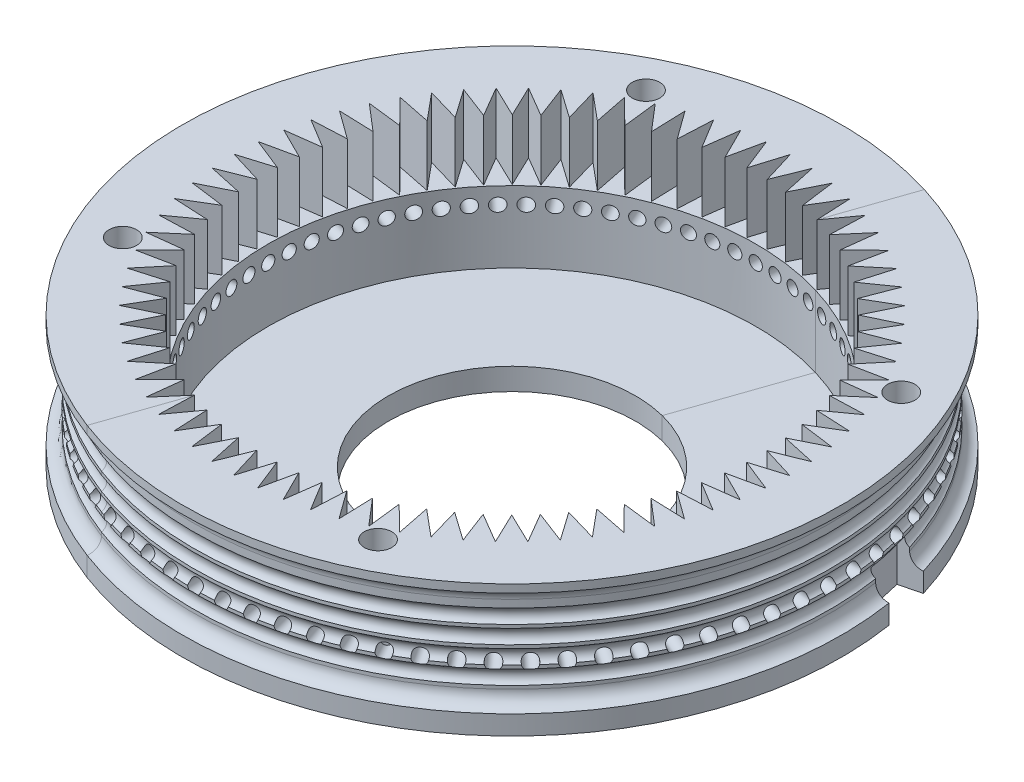
SolidWorks part; units mm, degrees
ref_plane "Front Plane" through (0, 0, 0) normal (0, 0, 1) x (1, 0, 0)
ref_plane "Top Plane" through (0, 0, 0) normal (0, 1, 0) x (1, 0, 0)
ref_plane "Right Plane" through (0, 0, 0) normal (1, 0, 0) x (0, 0, -1)
sketch "Sketch1" plane through (0, 0, 0) normal (0, 1, 0) x (1, 0, 0)
  circle A1 centre (0, 0) radius 23
extrude "Boss-Extrude1" add sketch "Sketch1" against normal blind 2
sketch "Sketch2" plane through (0, 0, 0) normal (0, 1, 0) x (1, 0, 0)
  circle A0 centre (0, 0) radius 30
  circle A1 centre (0, 0) radius 22.2
extrude "Boss-Extrude2" add sketch "Sketch2" along normal blind 12
sketch "Sketch3" plane through (0, 0, 0) normal (0, 1, 0) x (1, 0, 0)
  circle A0 centre (0, 0) radius 11.25
extrude "Cut-Extrude1" cut sketch "Sketch3" against normal blind 10 contours A0
ref_plane "Plane1" through (0, 12, 0) normal (0, 1, 0) x (1, 0, 0)
ref_plane "Plane2" through (0, -2, 0) normal (0, -1, 0) x (-1, 0, 0)
ref_plane "Plane3" through (0, 0, 0) normal (0, -1, 0) x (-1, 0, 0)
sketch "Sketch6" plane through (0, 0, 0) normal (1, 0, 0) x (0, 0, -1)
  line L0 (30.0526, 11.27) -> (30.6112, 11.27)
  line L1 (30.6112, 11.27) -> (30.6112, 1.7441)
  line L2 (30.6112, 6.507) -> (36.0017, 6.507) construction
  line L3 (30.6112, 1.7441) -> (30.0526, 1.7441)
  line L4 (28.9711, 9.6701) -> (28.9711, 9.363)
  line L5 (28.9711, 8.0701) -> (28.9711, 7.763)
  line L6 (28.9711, 6.4701) -> (28.9711, 6.163)
  line L7 (28.9711, 4.8701) -> (28.9711, 4.563)
  line L8 (28.9711, 3.2701) -> (28.9711, 2.963)
  line L9 (28.9711, 10.051) -> (28.9711, 9.6701)
  arc A0 (28.9711, 10.051) -> (30.0526, 11.27) centre (30.1988, 10.051) cw
  arc A1 (28.9711, 9.363) -> (28.9711, 8.0701) centre (29.3513, 8.7166) ccw
  arc A2 (28.9711, 7.763) -> (28.9711, 6.4701) centre (29.3513, 7.1166) ccw
  arc A3 (28.9711, 6.163) -> (28.9711, 4.8701) centre (29.3513, 5.5166) ccw
  arc A4 (28.9711, 4.563) -> (28.9711, 3.2701) centre (29.3513, 3.9166) ccw
  arc A5 (28.9711, 2.963) -> (30.0526, 1.7441) centre (30.1988, 2.963) ccw
  dimension "D2" = 1.6
  dimension "D3" = 1.6
  dimension "D4" = 1.6
ref_axis "Axis1" through (0, -2, 0) along (0, 1, 0)
sketch "Sketch10" plane through (0, 12, 0) normal (0, 1, 0) x (1, 0, 0)
  line L0 (8.2003, -23.949) -> (8.0956, -20.7964)
  line L1 (8.2003, -23.949) -> (7.2077, -21.0502) construction
  line L2 (8.2003, -23.949) -> (6.3506, -21.3939)
  line L3 (6.1946, -24.5444) -> (6.3506, -21.3939)
  line L5 (6.1946, -24.5444) -> (4.5623, -21.8453)
  line L6 (4.1466, -24.9721) -> (4.5623, -21.8453)
  line L7 (4.1466, -24.9721) -> (2.7427, -22.1474)
  line L8 (2.0703, -25.2292) -> (2.7427, -22.1474)
  line L9 (2.0703, -25.2292) -> (0.9044, -22.2983)
  line L10 (-0.0202, -25.314) -> (0.9044, -22.2983)
  line L11 (-0.0202, -25.314) -> (-0.9401, -22.2968)
  line L12 (-2.1106, -25.2259) -> (-0.9401, -22.2968)
  line L13 (-2.1106, -25.2259) -> (-2.7781, -22.143)
  line L14 (-4.1865, -24.9654) -> (-2.7781, -22.143)
  line L15 (-4.1865, -24.9654) -> (-4.5972, -21.838)
  line L16 (-6.2338, -24.5345) -> (-4.5972, -21.838)
  line L17 (-6.2338, -24.5345) -> (-6.3848, -21.3837)
  line L18 (-8.2386, -23.9359) -> (-6.3848, -21.3837)
  line L19 (-8.2386, -23.9359) -> (-8.1289, -20.7835)
  line L20 (-10.1871, -23.1738) -> (-8.1289, -20.7835)
  line L21 (-10.1871, -23.1738) -> (-9.8174, -20.0412)
  line L22 (-12.0659, -22.2534) -> (-9.8174, -20.0412)
  line L23 (-12.0659, -22.2534) -> (-11.4389, -19.162)
  line L24 (-13.8624, -21.181) -> (-11.4389, -19.162)
  line L25 (-13.8624, -21.181) -> (-12.9822, -18.152)
  line L26 (-15.5642, -19.9639) -> (-12.9822, -18.152)
  line L27 (-15.5642, -19.9639) -> (-14.4368, -17.0179)
  line L28 (-17.1596, -18.6104) -> (-14.4368, -17.0179)
  line L29 (-17.1596, -18.6104) -> (-15.7928, -15.7676)
  line L30 (-18.6378, -17.1298) -> (-15.7928, -15.7676)
  line L31 (-18.6378, -17.1298) -> (-17.041, -14.4096)
  line L32 (-19.9887, -15.5322) -> (-17.041, -14.4096)
  line L33 (-19.9887, -15.5322) -> (-18.1727, -12.9531)
  line L34 (-21.2031, -13.8285) -> (-18.1727, -12.9531)
  line L35 (-21.2031, -13.8285) -> (-19.1803, -11.4082)
  line L36 (-22.2726, -12.0304) -> (-19.1803, -11.4082)
  line L37 (-22.2726, -12.0304) -> (-20.0569, -9.7854)
  line L38 (-23.19, -10.15) -> (-20.0569, -9.7854)
  line L39 (-23.19, -10.15) -> (-20.7964, -8.0956)
  line L40 (-23.949, -8.2003) -> (-20.7964, -8.0956)
  line L41 (-23.949, -8.2003) -> (-21.3939, -6.3506)
  line L42 (-24.5444, -6.1946) -> (-21.3939, -6.3506)
  line L43 (-24.5444, -6.1946) -> (-21.8453, -4.5623)
  line L44 (-24.9721, -4.1466) -> (-21.8453, -4.5623)
  line L45 (-24.9721, -4.1466) -> (-22.1474, -2.7427)
  line L46 (-25.2292, -2.0703) -> (-22.1474, -2.7427)
  line L47 (-25.2292, -2.0703) -> (-22.2983, -0.9044)
  line L48 (-25.314, 0.0202) -> (-22.2983, -0.9044)
  line L49 (-25.314, 0.0202) -> (-22.2968, 0.9401)
  line L50 (-25.2259, 2.1106) -> (-22.2968, 0.9401)
  line L51 (-25.2259, 2.1106) -> (-22.143, 2.7781)
  line L52 (-24.9654, 4.1865) -> (-22.143, 2.7781)
  line L53 (-24.9654, 4.1865) -> (-21.838, 4.5972)
  line L54 (-24.5345, 6.2338) -> (-21.838, 4.5972)
  line L55 (-24.5345, 6.2338) -> (-21.3837, 6.3848)
  line L56 (-23.9359, 8.2386) -> (-21.3837, 6.3848)
  line L57 (-23.9359, 8.2386) -> (-20.7835, 8.1289)
  line L58 (-23.1738, 10.1871) -> (-20.7835, 8.1289)
  line L59 (-23.1738, 10.1871) -> (-20.0412, 9.8174)
  line L60 (-22.2534, 12.0659) -> (-20.0412, 9.8174)
  line L61 (-22.2534, 12.0659) -> (-19.162, 11.4389)
  line L62 (-21.181, 13.8624) -> (-19.162, 11.4389)
  line L63 (-21.181, 13.8624) -> (-18.152, 12.9822)
  line L64 (-19.9639, 15.5642) -> (-18.152, 12.9822)
  line L65 (-19.9639, 15.5642) -> (-17.0179, 14.4368)
  line L66 (-18.6104, 17.1596) -> (-17.0179, 14.4368)
  line L67 (-18.6104, 17.1596) -> (-15.7676, 15.7928)
  line L68 (-17.1298, 18.6378) -> (-15.7676, 15.7928)
  line L69 (-17.1298, 18.6378) -> (-14.4096, 17.041)
  line L70 (-15.5322, 19.9887) -> (-14.4096, 17.041)
  line L71 (-15.5322, 19.9887) -> (-12.9531, 18.1727)
  line L72 (-13.8285, 21.2031) -> (-12.9531, 18.1727)
  line L73 (-13.8285, 21.2031) -> (-11.4082, 19.1803)
  line L74 (-12.0304, 22.2726) -> (-11.4082, 19.1803)
  line L75 (-12.0304, 22.2726) -> (-9.7854, 20.0569)
  line L76 (-10.15, 23.19) -> (-9.7854, 20.0569)
  line L77 (-10.15, 23.19) -> (-8.0956, 20.7964)
  line L78 (-8.2003, 23.949) -> (-8.0956, 20.7964)
  line L79 (-8.2003, 23.949) -> (-6.3506, 21.3939)
  line L80 (-6.1946, 24.5444) -> (-6.3506, 21.3939)
  line L81 (-6.1946, 24.5444) -> (-4.5623, 21.8453)
  line L82 (-4.1466, 24.9721) -> (-4.5623, 21.8453)
  line L83 (-4.1466, 24.9721) -> (-2.7427, 22.1474)
  line L84 (-2.0703, 25.2292) -> (-2.7427, 22.1474)
  line L85 (-2.0703, 25.2292) -> (-0.9044, 22.2983)
  line L86 (0.0202, 25.314) -> (-0.9044, 22.2983)
  line L87 (0.0202, 25.314) -> (0.9401, 22.2968)
  line L88 (2.1106, 25.2259) -> (0.9401, 22.2968)
  line L89 (2.1106, 25.2259) -> (2.7781, 22.143)
  line L90 (4.1865, 24.9654) -> (2.7781, 22.143)
  line L91 (4.1865, 24.9654) -> (4.5972, 21.838)
  line L92 (6.2338, 24.5345) -> (4.5972, 21.838)
  line L93 (6.2338, 24.5345) -> (6.3848, 21.3837)
  line L94 (8.2386, 23.9359) -> (6.3848, 21.3837)
  line L95 (8.2386, 23.9359) -> (8.1289, 20.7835)
  line L96 (10.1871, 23.1738) -> (8.1289, 20.7835)
  line L97 (10.1871, 23.1738) -> (9.8174, 20.0412)
  line L98 (12.0659, 22.2534) -> (9.8174, 20.0412)
  line L99 (12.0659, 22.2534) -> (11.4389, 19.162)
  line L100 (13.8624, 21.181) -> (11.4389, 19.162)
  line L101 (13.8624, 21.181) -> (12.9822, 18.152)
  line L102 (15.5642, 19.9639) -> (12.9822, 18.152)
  line L103 (15.5642, 19.9639) -> (14.4368, 17.0179)
  line L104 (17.1596, 18.6104) -> (14.4368, 17.0179)
  line L105 (17.1596, 18.6104) -> (15.7928, 15.7676)
  line L106 (18.6378, 17.1298) -> (15.7928, 15.7676)
  line L107 (18.6378, 17.1298) -> (17.041, 14.4096)
  line L108 (19.9887, 15.5322) -> (17.041, 14.4096)
  line L109 (19.9887, 15.5322) -> (18.1727, 12.9531)
  line L110 (21.2031, 13.8285) -> (18.1727, 12.9531)
  line L111 (21.2031, 13.8285) -> (19.1803, 11.4082)
  line L112 (22.2726, 12.0304) -> (19.1803, 11.4082)
  line L113 (22.2726, 12.0304) -> (20.0569, 9.7854)
  line L114 (23.19, 10.15) -> (20.0569, 9.7854)
  line L115 (23.19, 10.15) -> (20.7964, 8.0956)
  line L116 (23.949, 8.2003) -> (20.7964, 8.0956)
  line L117 (23.949, 8.2003) -> (21.3939, 6.3506)
  line L118 (24.5444, 6.1946) -> (21.3939, 6.3506)
  line L119 (24.5444, 6.1946) -> (21.8453, 4.5623)
  line L120 (24.9721, 4.1466) -> (21.8453, 4.5623)
  line L121 (24.9721, 4.1466) -> (22.1474, 2.7427)
  line L122 (25.2292, 2.0703) -> (22.1474, 2.7427)
  line L123 (25.2292, 2.0703) -> (22.2983, 0.9044)
  line L124 (25.314, -0.0202) -> (22.2983, 0.9044)
  line L125 (25.314, -0.0202) -> (22.2968, -0.9401)
  line L126 (25.2259, -2.1106) -> (22.2968, -0.9401)
  line L127 (25.2259, -2.1106) -> (22.143, -2.7781)
  line L128 (24.9654, -4.1865) -> (22.143, -2.7781)
  line L129 (24.9654, -4.1865) -> (21.838, -4.5972)
  line L130 (24.5345, -6.2338) -> (21.838, -4.5972)
  line L131 (24.5345, -6.2338) -> (21.3837, -6.3848)
  line L132 (23.9359, -8.2386) -> (21.3837, -6.3848)
  line L133 (23.9359, -8.2386) -> (20.7835, -8.1289)
  line L134 (23.1738, -10.1871) -> (20.7835, -8.1289)
  line L135 (23.1738, -10.1871) -> (20.0412, -9.8174)
  line L136 (22.2534, -12.0659) -> (20.0412, -9.8174)
  line L137 (22.2534, -12.0659) -> (19.162, -11.4389)
  line L138 (21.181, -13.8624) -> (19.162, -11.4389)
  line L139 (21.181, -13.8624) -> (18.152, -12.9822)
  line L140 (19.9639, -15.5642) -> (18.152, -12.9822)
  line L141 (19.9639, -15.5642) -> (17.0179, -14.4368)
  line L142 (18.6104, -17.1596) -> (17.0179, -14.4368)
  line L143 (18.6104, -17.1596) -> (15.7676, -15.7928)
  line L144 (17.1298, -18.6378) -> (15.7676, -15.7928)
  line L145 (17.1298, -18.6378) -> (14.4096, -17.041)
  line L146 (15.5322, -19.9887) -> (14.4096, -17.041)
  line L147 (15.5322, -19.9887) -> (12.9531, -18.1727)
  line L148 (13.8285, -21.2031) -> (12.9531, -18.1727)
  line L149 (13.8285, -21.2031) -> (11.4082, -19.1803)
  line L150 (12.0304, -22.2726) -> (11.4082, -19.1803)
  line L151 (12.0304, -22.2726) -> (9.7854, -20.0569)
  line L152 (10.15, -23.19) -> (9.7854, -20.0569)
  line L153 (10.15, -23.19) -> (8.0956, -20.7964)
  line L184 (7.2077, -21.0502) -> (8.5243, -24.8951) construction
  point P235 (0, 0)
  dimension "D1" = 17
extrude "Cut-Extrude8" cut sketch "Sketch10" against normal blind 5.5
sketch "Sketch5" plane through (0, 12, 0) normal (0, 1, 0) x (1, 0, 0)
  line L0 (0, 0) -> (20.0775, 9.7954) construction
  line L1 (20.0775, 9.7954) -> (26.9622, 13.1544) construction
  circle A1 centre (0, 0) radius 30 construction
  circle A2 centre (23.8167, 11.6197) radius 1.25
  circle A3 centre (11.6197, -23.8167) radius 1.25
  circle A5 centre (-23.8167, -11.6197) radius 1.25
  circle A7 centre (-11.6197, 23.8167) radius 1.25
  point P21 (0, 0)
  dimension "D1" = 4
extrude "Cut-Extrude3" cut sketch "Sketch5" against normal through all
sketch "Sketch8" plane through (0, 0, 0) normal (0, -1, 0) x (-1, 0, 0)
  circle A0 centre (-23.8167, 11.6197) radius 2.5
  circle A1 centre (11.6197, 23.8167) radius 2.5
  circle A2 centre (23.8167, -11.6197) radius 2.5
  circle A3 centre (-11.6197, -23.8167) radius 2.5
  point P11 (0, 0)
extrude "Cut-Extrude5" cut sketch "Sketch8" against normal blind 2
ref_plane "Plane4" through (0, 0, 0) normal (0, 1, 0) x (1, 0, 0)
revolve "Cut-Revolve1" cut sketch "Sketch6" angle 360 about axis through (0, -2, 0) along (0, 1, 0)
sketch "Sketch12" plane through (0, -2, 0) normal (0, -1, 0) x (-1, 0, 0)
  line L2 (-19.6103, 3.4061) -> (-22.6044, 3.9868)
  line L3 (-19.1966, 5.5081) -> (-22.0729, 6.2962)
  line L8 (-22.7811, -2.8065) -> (-13.2828, -1.9137)
  line L9 (-19.2445, 12.5101) -> (-11.1512, 7.8264)
  line L11 (-13.2828, -1.9137) -> (-11.1512, 7.8264)
  arc A0 (-19.2445, 12.5101) -> (-22.0729, 6.2962) centre (0, 0) ccw
  arc A1 (-22.6044, 3.9868) -> (-22.7811, -2.8065) centre (0, 0) ccw
  arc A10 (-19.6103, 3.4061) -> (-19.1966, 5.5081) centre (-16.1341, 3.8136) ccw
extrude "Boss-Extrude3" add sketch "Sketch12" along normal blind 3
sketch "Sketch13" plane through (0, -2, 0) normal (0, -1, 0) x (-1, 0, 0)
  circle A0 centre (-16.1341, 3.8136) radius 3.5
extrude "Cut-Extrude9" cut sketch "Sketch13" against normal blind 3 contours A0
ref_plane "Plane5" through (0, 0, 0) normal (0, -1, 0) x (-1, 0, 0)
sketch "Sketch15" plane through (0, 0, 0) normal (0, -1, 0) x (-1, 0, 0)
  line L0 (-27.6851, 4.3056) -> (-29.0627, 4.5727)
  line L1 (-26.7661, 8.2772) -> (-28.1306, 8.6203)
  line L2 (-29.0627, 4.5727) -> (-29.8955, 4.7341)
  line L3 (-28.1306, 8.6203) -> (-29.0951, 8.8628)
  line L4 (-29.0951, 8.8628) -> (-29.8955, 4.7341)
  line L5 (-27.6851, 4.3056) -> (-26.7661, 8.2772)
extrude "Cut-Extrude10" cut sketch "Sketch15" against normal blind 4
sketch "Sketch16" plane through (0, 12, 0) normal (0, 1, 0) x (1, 0, 0)
  line L0 (0, 0) -> (-20.0412, 9.8174) construction
  line L1 (-22.2534, 12.0659) -> (-20.0412, 9.8174) construction
  line L2 (-20.0412, 9.8174) -> (-23.1738, 10.1871) construction
  line L3 (-20.0412, 9.8174) -> (-26.9412, 13.1974) construction
  line L4 (-20.0412, 9.8174) -> (-22.7353, 11.1371) construction
  circle A0 centre (0, 0) radius 30 construction
  circle A1 centre (-22.7353, 11.1371) radius 0.6
  circle A2 centre (-21.738, 12.9766) radius 0.6
  circle A3 centre (-20.5921, 14.7274) radius 0.6
  circle A4 centre (-19.3056, 16.3775) radius 0.6
  circle A5 centre (-17.8872, 17.9158) radius 0.6
  circle A6 centre (-16.3467, 19.3318) radius 0.6
  circle A7 centre (-14.6944, 20.6156) radius 0.6
  circle A8 centre (-12.9418, 21.7587) radius 0.6
  circle A10 centre (-9.1839, 23.5921) radius 0.6
  circle A11 centre (-7.2044, 24.2699) radius 0.6
  circle A12 centre (-5.1756, 24.7819) radius 0.6
  circle A13 centre (-3.1114, 25.1247) radius 0.6
  circle A14 centre (-1.026, 25.2958) radius 0.6
  circle A15 centre (1.0664, 25.2941) radius 0.6
  circle A16 centre (3.1516, 25.1197) radius 0.6
  circle A17 centre (5.2152, 24.7736) radius 0.6
  circle A18 centre (7.2431, 24.2583) radius 0.6
  circle A19 centre (9.2216, 23.5774) radius 0.6
  circle A20 centre (11.1371, 22.7353) radius 0.6
  circle A21 centre (12.9766, 21.738) radius 0.6
  circle A22 centre (14.7274, 20.5921) radius 0.6
  circle A23 centre (16.3775, 19.3056) radius 0.6
  circle A24 centre (17.9158, 17.8872) radius 0.6
  circle A25 centre (19.3318, 16.3467) radius 0.6
  circle A26 centre (20.6156, 14.6944) radius 0.6
  circle A27 centre (21.7587, 12.9418) radius 0.6
  circle A29 centre (23.5921, 9.1839) radius 0.6
  circle A30 centre (24.2699, 7.2044) radius 0.6
  circle A31 centre (24.7819, 5.1756) radius 0.6
  circle A32 centre (25.1247, 3.1114) radius 0.6
  circle A33 centre (25.2958, 1.026) radius 0.6
  circle A34 centre (25.2941, -1.0664) radius 0.6
  circle A35 centre (25.1197, -3.1516) radius 0.6
  circle A36 centre (24.7736, -5.2152) radius 0.6
  circle A37 centre (24.2583, -7.2431) radius 0.6
  circle A38 centre (23.5774, -9.2216) radius 0.6
  circle A39 centre (22.7353, -11.1371) radius 0.6
  circle A40 centre (21.738, -12.9766) radius 0.6
  circle A41 centre (20.5921, -14.7274) radius 0.6
  circle A42 centre (19.3056, -16.3775) radius 0.6
  circle A43 centre (17.8872, -17.9158) radius 0.6
  circle A44 centre (16.3467, -19.3318) radius 0.6
  circle A45 centre (14.6944, -20.6156) radius 0.6
  circle A46 centre (12.9418, -21.7587) radius 0.6
  circle A48 centre (9.1839, -23.5921) radius 0.6
  circle A49 centre (7.2044, -24.2699) radius 0.6
  circle A50 centre (5.1756, -24.7819) radius 0.6
  circle A51 centre (3.1114, -25.1247) radius 0.6
  circle A52 centre (1.026, -25.2958) radius 0.6
  circle A53 centre (-1.0664, -25.2941) radius 0.6
  circle A54 centre (-3.1516, -25.1197) radius 0.6
  circle A55 centre (-5.2152, -24.7736) radius 0.6
  circle A56 centre (-7.2431, -24.2583) radius 0.6
  circle A57 centre (-9.2216, -23.5774) radius 0.6
  circle A58 centre (-11.1371, -22.7353) radius 0.6
  circle A59 centre (-12.9766, -21.738) radius 0.6
  circle A60 centre (-14.7274, -20.5921) radius 0.6
  circle A61 centre (-16.3775, -19.3056) radius 0.6
  circle A62 centre (-17.9158, -17.8872) radius 0.6
  circle A63 centre (-19.3318, -16.3467) radius 0.6
  circle A64 centre (-20.6156, -14.6944) radius 0.6
  circle A65 centre (-21.7587, -12.9418) radius 0.6
  circle A67 centre (-23.5921, -9.1839) radius 0.6
  circle A68 centre (-24.2699, -7.2044) radius 0.6
  circle A69 centre (-24.7819, -5.1756) radius 0.6
  circle A70 centre (-25.1247, -3.1114) radius 0.6
  circle A71 centre (-25.2958, -1.026) radius 0.6
  circle A72 centre (-25.2941, 1.0664) radius 0.6
  circle A73 centre (-25.1197, 3.1516) radius 0.6
  circle A74 centre (-24.7736, 5.2152) radius 0.6
  circle A75 centre (-24.2583, 7.2431) radius 0.6
  circle A76 centre (-23.5774, 9.2216) radius 0.6
  circle A77 centre (-11.1008, 22.7531) radius 0.6 [skipped]
  circle A78 centre (-22.7531, -11.1008) radius 0.6 [skipped]
  circle A79 centre (11.1008, -22.7531) radius 0.6 [skipped]
  circle A80 centre (22.7531, 11.1008) radius 0.6 [skipped]
  point P165 (0, 0)
  dimension "D1" = 76
extrude "Cut-Extrude11" [suppressed] cut sketch "Sketch16" against normal blind 11.2
ref_plane "Plane6" through (0.9044, 12, 22.2983) normal (0, 1, 0) x (1, 0, 0)
sketch "Sketch17" plane through (0, 0, 0) normal (0, 0, 1) x (1, 0, 0)
  line L0 (0, 0) -> (0, 5) construction
  circle A0 centre (0, 5) radius 0.6
extrude "Cut-Extrude12" cut sketch "Sketch17" along normal blind 33 contours A0
pattern_circular "CirPattern1" count 76 over 360 about axis through (0, -2, 0) along (0, 1, 0) of "Cut-Extrude12"
sketch "Sketch18" plane through (0, 12, 0) normal (0, 1, 0) x (1, 0, 0)
  line L0 (6.3848, 21.3837) -> (-8.1289, -20.7835)
ref_plane "Plane7" through (-0.872, 0, -0.3001) normal (-0.9456, 0, -0.3255) x (-0.3255, 0, 0.9456)
split "Split1" trim tools "Plane7" bodies to split 123 resulting bodies 125 126
